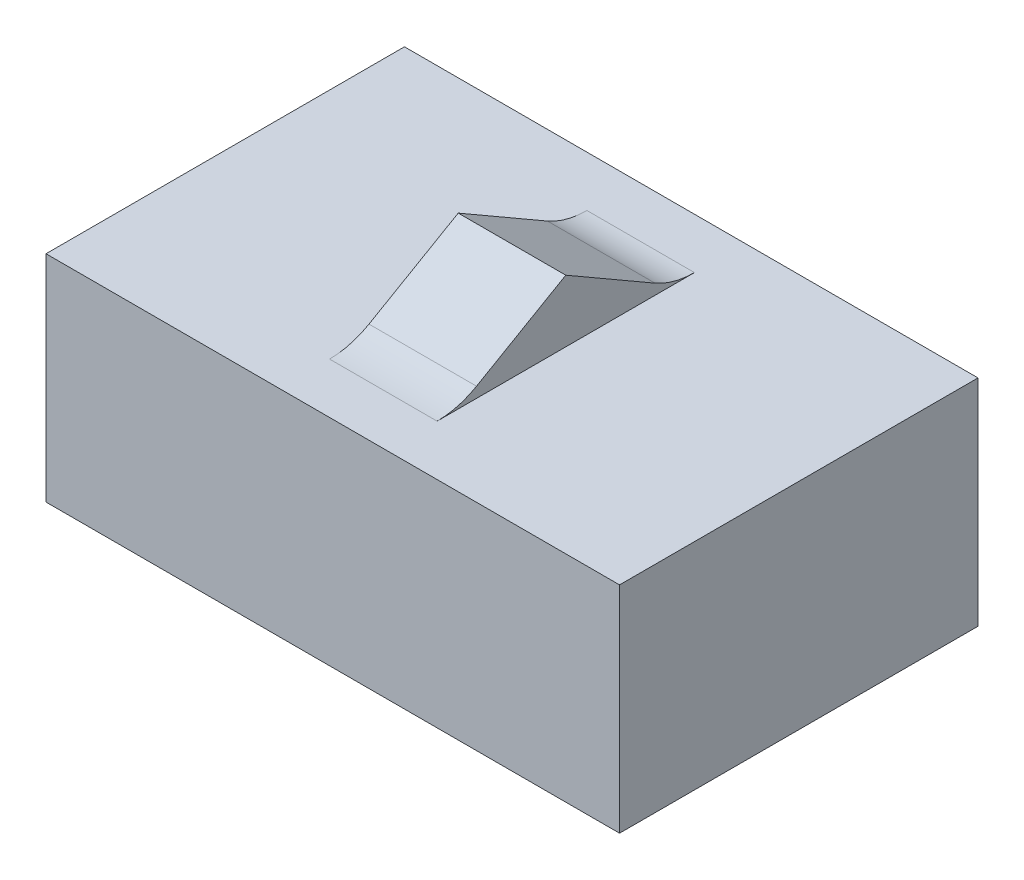
SolidWorks part; units mm, degrees
ref_plane "前视基准面" through (0, 0, 0) normal (0, 0, 1) x (1, 0, 0)
ref_plane "上视基准面" through (0, 0, 0) normal (0, 1, 0) x (1, 0, 0)
ref_plane "右视基准面" through (0, 0, 0) normal (1, 0, 0) x (0, 0, -1)
sketch "草图1" plane through (0, 0, 0) normal (0, 1, 0) x (1, 0, 0)
  line L1 (4, 2.5) -> (-4, 2.5)
  line L2 (4, 2.5) -> (4, -2.5)
  line L3 (4, -2.5) -> (-4, -2.5)
  line L4 (-4, 2.5) -> (-4, -2.5)
  line L5 (4, 2.5) -> (-4, -2.5) construction
  line L6 (4, -2.5) -> (-4, 2.5) construction
  point P0 (0, 0)
  dimension "D1" = 5
  dimension "D2" = 8
extrude "凸台-拉伸1" add sketch "草图1" along normal blind 3
sketch "草图2" plane through (0, 0, 0) normal (1, 0, 0) x (0, 0, -1)
  line L0 (0, 0) -> (0, 3.8009) construction
  line L1 (0, 3.866) -> (-1.5, 3)
  line L2 (-2.5, 3) -> (2.5, 3) construction
  line L3 (-1.5, 3) -> (1.5, 3)
  line L6 (0, 3.866) -> (1.5, 3)
  dimension "D1" = 30
  dimension "D2" = 3
extrude "凸台-拉伸2" add sketch "草图2" along normal mid plane 1.5
fillet "圆角1" radius 1.1 2 edges at (0, 3, 1.5) (0, 3, -1.5)
other "成形工具1"
sketch "方向草图" plane through (0, 3, 0) normal (0, 1, 0) x (1, 0, 0)
  line L0 (1.5, -1.7947) -> (-1.5, -1.7947) construction
  line L1 (-1.5, -1.7947) -> (-1.5, 1.5) construction
  line L2 (1.5, 1.5) -> (-1.5, 1.5) construction
  line L3 (1.5, -1.7947) -> (1.5, 1.5) construction
  line L4 (-4, 2.5) -> (-4, -2.5) construction
  line L5 (-4, -2.5) -> (4, -2.5) construction
  line L6 (4, -2.5) -> (4, 2.5) construction
  line L7 (4, 2.5) -> (-4, 2.5) construction
  line L8 (1.5, -1.7947) -> (-1.5, -1.7947)
  line L9 (-1.5, -1.7947) -> (-1.5, 1.5)
  line L10 (1.5, 1.5) -> (-1.5, 1.5)
  line L11 (1.5, -1.7947) -> (1.5, 1.5)
  line L12 (-4, 2.5) -> (-4, -2.5) construction
  line L13 (-4, -2.5) -> (4, -2.5) construction
  line L14 (4, -2.5) -> (4, 2.5) construction
  line L15 (4, 2.5) -> (-4, 2.5) construction
  point P6 (0, 0)
